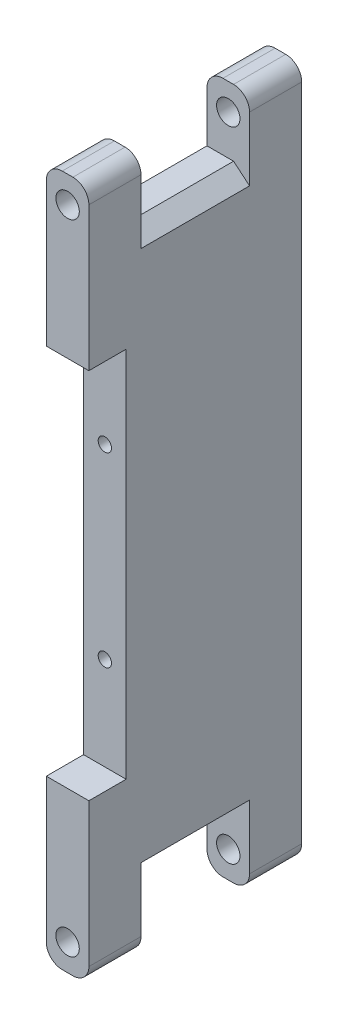
SolidWorks part; units mm, degrees
ref_plane "Front Plane" through (0, 0, 0) normal (0, 0, 1) x (1, 0, 0)
ref_plane "Top Plane" through (0, 0, 0) normal (0, 1, 0) x (1, 0, 0)
ref_plane "Right Plane" through (0, 0, 0) normal (1, 0, 0) x (0, 0, -1)
sketch "Sketch1" plane through (0, 0, 0) normal (0, 0, 1) x (1, 0, 0)
  line L1 (-4, 65) -> (4, 65)
  line L2 (-4, 65) -> (-4, -65)
  line L3 (-4, -65) -> (4, -65)
  line L4 (4, 65) -> (4, -65)
  line L5 (-4, 65) -> (4, -65) construction
  line L6 (-4, -65) -> (4, 65) construction
  point P0 (0, 0)
  dimension "D1" = 8
  dimension "D2" = 130
extrude "Boss-Extrude1" add sketch "Sketch1" against normal blind 40
sketch "Sketch2" plane through (4, 0, 0) normal (1, 0, 0) x (0, 0, -1)
  line L0 (40, 65) -> (0, 65) construction
  line L1 (9.8, 77.5) -> (30.2, 77.5)
  line L2 (9.8, 77.5) -> (9.8, 52.5)
  line L3 (9.8, 52.5) -> (30.2, 52.5)
  line L4 (30.2, 77.5) -> (30.2, 52.5)
  line L5 (9.8, 77.5) -> (30.2, 52.5) construction
  line L6 (9.8, 52.5) -> (30.2, 77.5) construction
  line L7 (0, 0) -> (54.2084, 0) construction
  line L8 (9.8, -52.5) -> (30.2, -77.5) construction
  line L9 (9.8, -77.5) -> (30.2, -52.5) construction
  line L10 (30.2, -77.5) -> (30.2, -52.5)
  line L11 (9.8, -52.5) -> (30.2, -52.5)
  line L12 (9.8, -77.5) -> (9.8, -52.5)
  line L13 (9.8, -77.5) -> (30.2, -77.5)
  line L14 (40, -65) -> (40, 65) construction
  point P0 (20, 65)
  point P14 (20, -65)
  dimension "D1" = 25
  dimension "D2" = 9.8
extrude "Cut-Extrude1" cut sketch "Sketch2" against normal through all
fillet "Fillet1" radius 3 8 edges at (-4, -65, -35.1) (4, -65, -35.1) (-4, -65, -4.9) (4, -65, -4.9) (-4, 65, -4.9) (-4, 65, -35.1) (4, 65, -35.1) (4, 65, -4.9)
sketch "Sketch3" plane through (0, 0, 0) normal (0, 0, 1) x (1, 0, 0)
  line L0 (0, 0) -> (0, 60) construction
  line L1 (1, 65) -> (-1, 65) construction
  line L2 (0, 0) -> (14.6507, 0) construction
  circle A0 centre (0, 60) radius 2.2
  circle A1 centre (0, -60) radius 2.2
  dimension "D1" = 4.4
  dimension "D2" = 5
extrude "Cut-Extrude2" cut sketch "Sketch3" against normal through all
sketch "Sketch4" plane through (0, 0, 0) normal (0, 0, 1) x (1, 0, 0)
  line L1 (-28.0521, 35) -> (28.0521, 35)
  line L2 (-28.0521, 35) -> (-28.0521, -35)
  line L3 (-28.0521, -35) -> (28.0521, -35)
  line L4 (28.0521, 35) -> (28.0521, -35)
  line L5 (-28.0521, 35) -> (28.0521, -35) construction
  line L6 (-28.0521, -35) -> (28.0521, 35) construction
  point P0 (0, 0)
  dimension "D1" = 70
extrude "Cut-Extrude3" cut sketch "Sketch4" against normal blind 7
sketch "Sketch5" plane through (0, 0, -7) normal (0, 0, 1) x (1, 0, 0)
  line L0 (0, -17.5) -> (0, 17.5) construction
  circle A0 centre (0, 17.5) radius 1.25
  circle A1 centre (0, -17.5) radius 1.25
  dimension "D1" = 17.5
  dimension "D3" = 2.5
  dimension "D2" = 17.5
extrude "Cut-Extrude4" cut sketch "Sketch5" against normal blind 15
chamfer "Chamfer1" distance 3 angle 40 2 edges at (4, 52.5, -20) (4, -52.5, -20)
